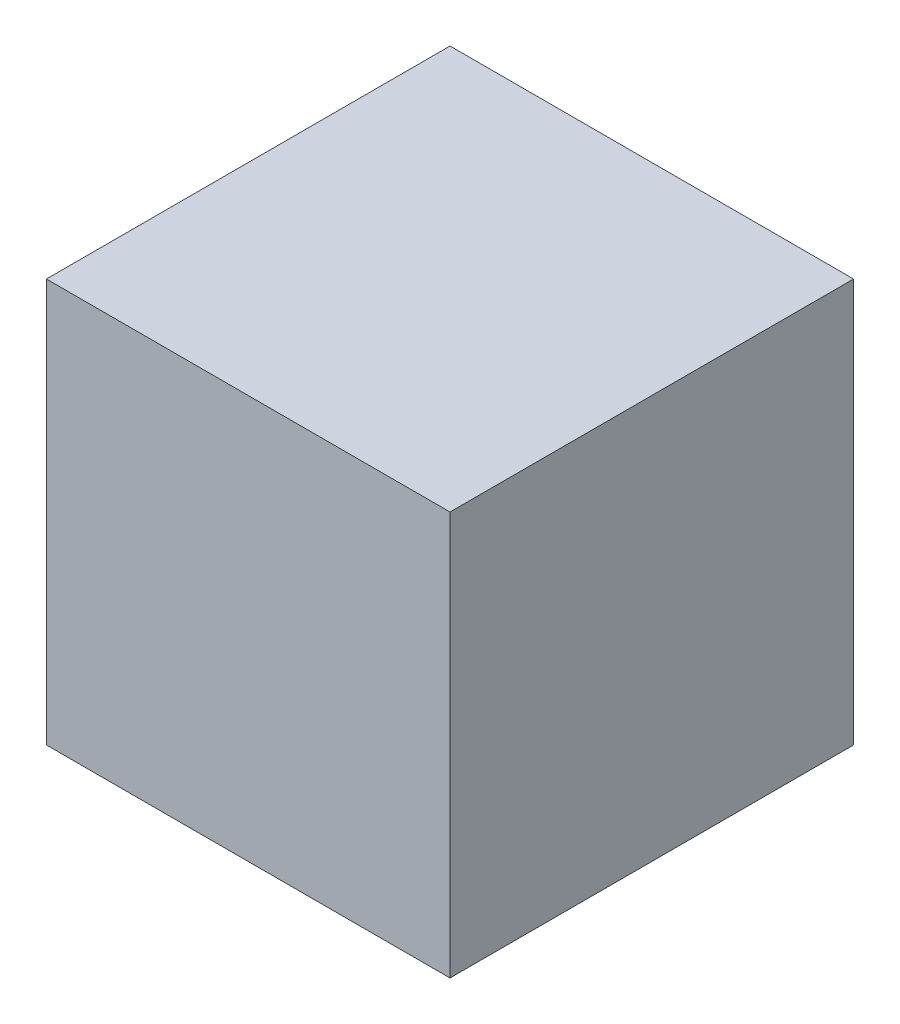
SolidWorks part; units mm, degrees
ref_plane "Front Plane" through (0, 0, 0) normal (0, 0, 1) x (1, 0, 0)
ref_plane "Top Plane" through (0, 0, 0) normal (0, 1, 0) x (1, 0, 0)
ref_plane "Right Plane" through (0, 0, 0) normal (1, 0, 0) x (0, 0, -1)
sketch "Sketch1" plane through (0, 0, 0) normal (0, 0, 1) x (1, 0, 0)
  line L1 (-5, -5) -> (5, -5)
  line L2 (-5, -5) -> (-5, 5)
  line L3 (-5, 5) -> (5, 5)
  line L4 (5, -5) -> (5, 5)
  line L5 (-5, -5) -> (5, 5) construction
  line L6 (-5, 5) -> (5, -5) construction
  point P0 (0, 0)
  dimension "D1" = 10
extrude "Boss-Extrude1" add sketch "Sketch1" along normal mid plane 10
hole_wizard "M3x0.5 Tapped Hole1" positions "Sketch3" profile "Sketch4" tap size "M3x0.5" standard "ANSI Metric"
sketch "Sketch3" plane through (0, -5, 0) normal (0, -1, 0) x (-1, 0, 0)
  line L0 (-5, -5) -> (-5, 5) construction
  point P0 (-2.5, 0)
  point P2 (2.5, 0)
  point P7 (0, 0)
  point P9 (0, 0)
  dimension "D1" = 5
  dimension "D2" = 2.5
sketch "Sketch4" plane through (2.5, -5, 0) normal (1, 0, 0) x (0, 0, -1)
  line L0 (0, 0) -> (0, 7.5)
  line L1 (0, 7.5) -> (1.25, 6.7489)
  line L2 (1.25, 6.7489) -> (1.25, 0)
  line L5 (1.25, 0) -> (0, 0)
  line L10 (0, 7.5) -> (-1.25, 6.7489) construction
  line L11 (0, -6.35) -> (0, 107.95) construction
  dimension "Tap Drill Dia." = 2.5
  dimension "Tap Drill Depth" = 7.5
  dimension "Drill Angle" = 118
cosmetic thread "Hole Thread1" parameters "D1"=6, "D2"=3
cosmetic thread "Hole Thread2" parameters "D1"=6, "D2"=3
